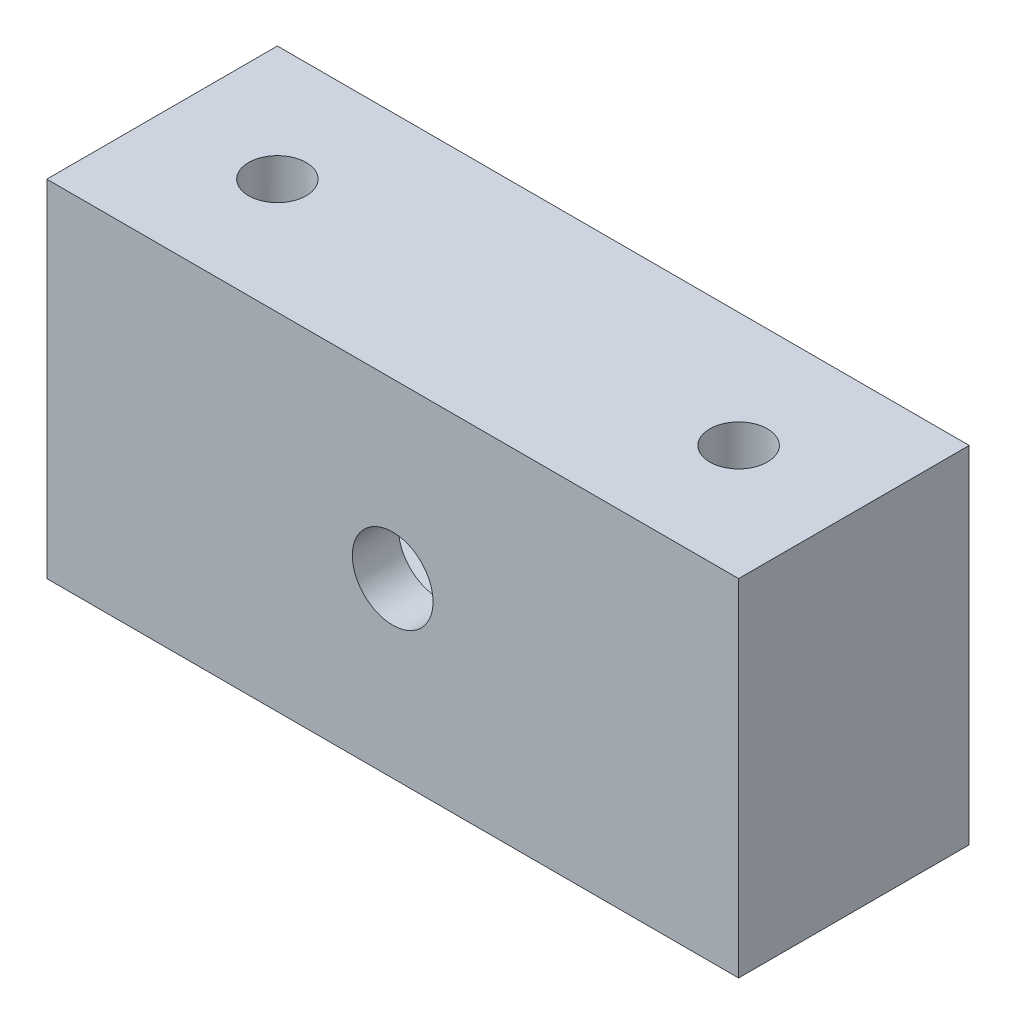
SolidWorks part; units mm, degrees
material "2024-T3"
ref_plane "Plan de face" through (0, 0, 0) normal (0, 0, 1) x (1, 0, 0)
ref_plane "Plan de dessus" through (0, 0, 0) normal (0, 1, 0) x (1, 0, 0)
ref_plane "Plan de droite" through (0, 0, 0) normal (1, 0, 0) x (0, 0, -1)
sketch "Esquisse1" plane through (0, 0, 0) normal (0, 0, 1) x (1, 0, 0)
  line L1 (-15, 7.5) -> (15, 7.5)
  line L2 (-15, 7.5) -> (-15, -7.5)
  line L3 (-15, -7.5) -> (15, -7.5)
  line L4 (15, 7.5) -> (15, -7.5)
  line L5 (-15, 7.5) -> (15, -7.5) construction
  line L6 (-15, -7.5) -> (15, 7.5) construction
  point P0 (0, 0)
  dimension "D1" = 30
  dimension "D2" = 15
extrude "Boss.-Extru.1" add sketch "Esquisse1" along normal blind 10
sketch "Esquisse2" plane through (0, 0, 0) normal (0, 0, -1) x (-1, 0, 0)
  line L14 (-12, -4.5) -> (12, -4.5)
  line L15 (12, -4.5) -> (12, 4.5)
  line L16 (12, 4.5) -> (-12, 4.5)
  line L17 (-12, 4.5) -> (-12, -4.5)
  line L18 (-12, -4.5) -> (12, -4.5)
  line L19 (12, -4.5) -> (12, 4.5)
  line L20 (12, 4.5) -> (-12, 4.5)
  line L21 (-12, 4.5) -> (-12, -4.5)
  dimension "D1" = 3
extrude "Enlèv. mat.-Extru.1" cut sketch "Esquisse2" against normal blind 8
fillet "Congé1" radius 2 4 edges at (-12, -4.5, 4) (12, -4.5, 4) (-12, 4.5, 4) (12, 4.5, 4)
sketch "Esquisse3" plane through (0, 0, 8) normal (0, 0, -1) x (-1, 0, 0)
  circle A0 centre (0, 0) radius 1.75
  dimension "D1" = 3.5
extrude "Enlèv. mat.-Extru.2" cut sketch "Esquisse3" against normal through all
sketch "Esquisse4" plane through (0, -7.5, 0) normal (0, -1, 0) x (1, 0, 0)
  line L0 (-15, 5) -> (15, 5) construction
  line L1 (-15, 10) -> (-15, 0) construction
  line L2 (15, 10) -> (15, 0) construction
  line L3 (-15, 10) -> (15, 10) construction
  line L4 (0, 0) -> (0, 10) construction
  line L5 (-15, 0) -> (15, 0) construction
  circle A0 centre (-10, 5) radius 1.25
  circle A1 centre (10, 5) radius 1.25
  dimension "D2" = 20
  dimension "D3" = 10
  dimension "D4" = 2.5
  dimension "D5" = 2.5
  dimension "D1" = 5
hole_wizard "Trou taraudé M31" positions "Esquisse6" profile "Esquisse5" tap size "M3" standard "ISO" end condition through all
sketch "Esquisse6" plane through (0, -7.5, 0) normal (0, -1, 0) x (-1, 0, 0)
  point P0 (-10, -5)
sketch "Esquisse5" plane through (10, -7.5, 5) normal (1, 0, 0) x (0, 0, -1)
  line L0 (0, 0) -> (0, 15)
  line L1 (0, 15) -> (1.25, 15)
  line L2 (1.25, 15) -> (1.25, 0)
  line L5 (1.25, 0) -> (0, 0)
  line L11 (0, -6.35) -> (0, 107.95) construction
  dimension "Diamètre du trou pour taraudage jusqu'au prochain" = 2.5
  dimension "Profondeur du trou pour taraudage jusqu'au prochain" = 15
cosmetic thread "Filetage de perçage1" parameters "D2"=3
hole_wizard "Trou taraudé M32" positions "Esquisse9" profile "Esquisse7" tap size "M3" standard "ISO" end condition through all
sketch "Esquisse9" plane through (0, -7.5, 0) normal (0, -1, 0) x (-1, 0, 0)
  point P0 (10, -5)
sketch "Esquisse7" plane through (-10, -7.5, 5) normal (1, 0, 0) x (0, 0, -1)
  line L0 (0, 0) -> (0, 15)
  line L1 (0, 15) -> (1.25, 15)
  line L2 (1.25, 15) -> (1.25, 0)
  line L5 (1.25, 0) -> (0, 0)
  line L11 (0, -6.35) -> (0, 107.95) construction
  dimension "Diamètre du trou pour taraudage jusqu'au prochain" = 2.5
  dimension "Profondeur du trou pour taraudage jusqu'au prochain" = 15
cosmetic thread "Filetage de perçage2" parameters "D2"=3
